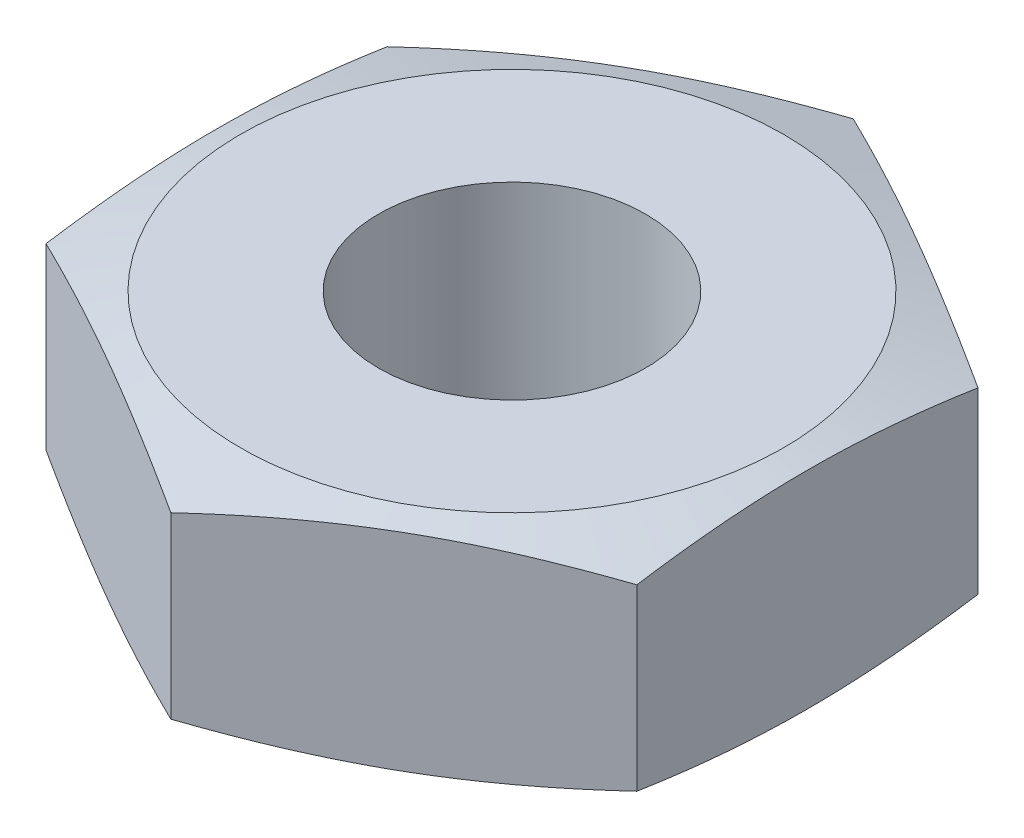
SolidWorks part; units mm, degrees
ref_plane "Front Plane" through (0, 0, 0) normal (0, 0, 1) x (1, 0, 0)
ref_plane "Top Plane" through (0, 0, 0) normal (0, 1, 0) x (1, 0, 0)
ref_plane "Right Plane" through (0, 0, 0) normal (1, 0, 0) x (0, 0, -1)
sketch "Sketch1" plane through (0, 0, 0) normal (0, 1, 0) x (1, 0, 0)
  line L0 (0, 0) -> (0, 3.6662) construction
  line L1 (0, -3.6662) -> (3.175, -1.8331)
  line L2 (3.175, -1.8331) -> (3.175, 1.8331)
  line L3 (3.175, 1.8331) -> (0, 3.6662)
  line L4 (0, 3.6662) -> (-3.175, 1.8331)
  line L5 (-3.175, 1.8331) -> (-3.175, -1.8331)
  line L6 (-3.175, -1.8331) -> (0, -3.6662)
  circle A0 centre (0, 0) radius 3.175 construction
  circle A1 centre (0, 0) radius 1.4351
  dimension "D2" = 2.8702
  dimension "D1" = 6.35
extrude "Boss-Extrude1" add sketch "Sketch1" along normal blind 2.3813
sketch "Sketch2" plane through (0, 0, 0) normal (1, 0, 0) x (0, 0, -1)
  line L0 (2.9182, 2.3813) -> (3.6662, 2.1515)
  line L1 (1.8331, 2.3813) -> (3.6662, 2.3813) construction
  line L2 (3.6662, 2.3813) -> (3.6662, 0) construction
  line L3 (3.6662, 2.1515) -> (3.6662, 2.3813)
  line L4 (3.6662, 2.3813) -> (2.9182, 2.3813)
  line L5 (2.9182, 2.3813) -> (2.9182, 0) construction
  line L6 (1.8331, 0) -> (3.6662, 0) construction
  line L7 (2.9182, 0) -> (3.6662, 0)
  line L8 (3.6662, 0) -> (3.6662, 0.2298)
  line L9 (3.6662, 0.2298) -> (2.9182, 0)
  line L10 (0, 0) -> (0, 2.3813) construction
  line L11 (-1.8331, 2.3813) -> (1.8331, 2.3813) construction
revolve "Cut-Revolve1" cut sketch "Sketch2" angle 360 about L10
